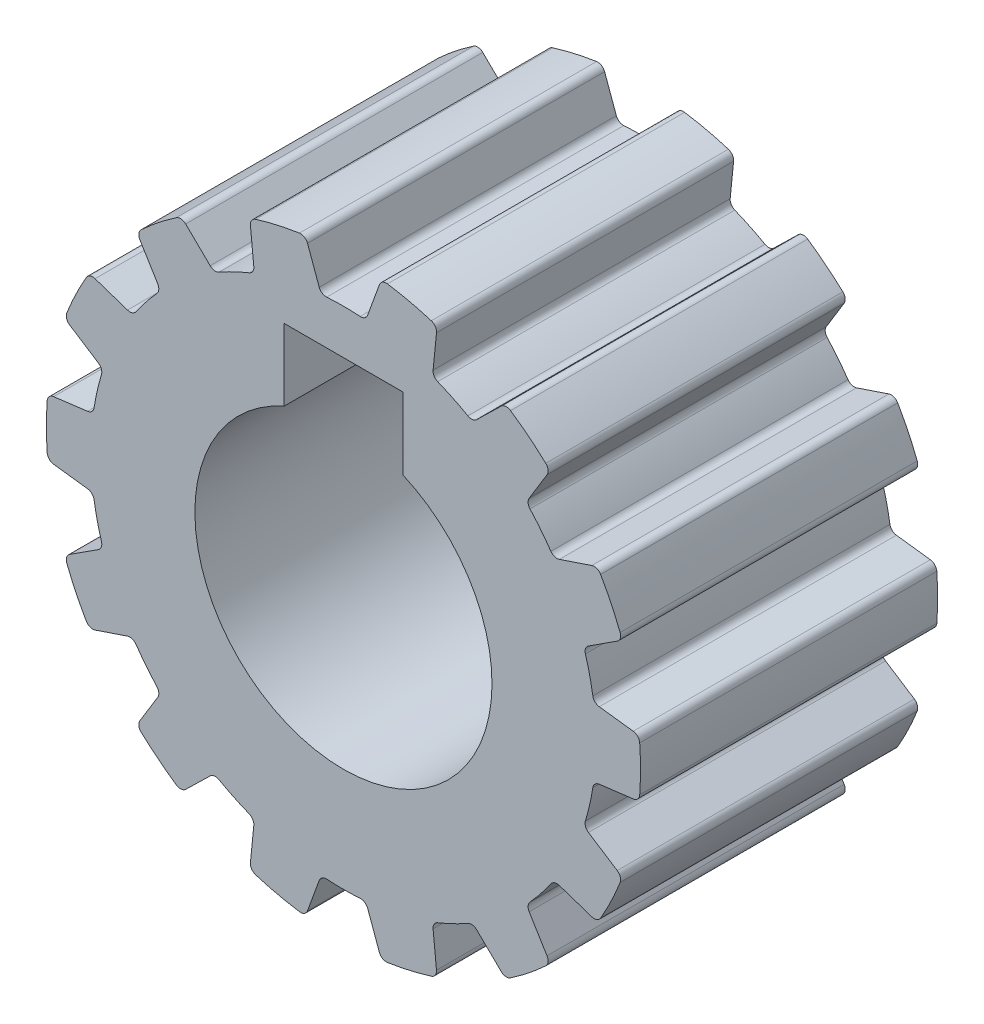
SolidWorks part; units mm, degrees
ref_plane "Front Plane" through (0, 0, 0) normal (0, 0, 1) x (1, 0, 0)
ref_plane "Top Plane" through (0, 0, 0) normal (0, 1, 0) x (1, 0, 0)
ref_plane "Right Plane" through (0, 0, 0) normal (1, 0, 0) x (0, 0, -1)
sketch "Sketch1" plane through (0, 0, 0) normal (0, 0, 1) x (1, 0, 0)
  line L0 (0, 0) -> (0, 15.3637) construction
  line L2 (-2, 7) -> (2, 7)
  line L3 (-2, 7) -> (-2, 4.5826)
  line L5 (2, 7) -> (2, 4.5826)
  circle A0 centre (0, 0) radius 10
  arc A1 (-2, 4.5826) -> (2, 4.5826) centre (0, 0) ccw
  dimension "D1" = 20
  dimension "D2" = 10
  dimension "D3" = 7
  dimension "D4" = 4
extrude "Boss-Extrude1" add sketch "Sketch1" along normal blind 10
sketch "Sketch2" plane through (0, 0, 10) normal (0, 0, 1) x (1, 0, 0)
  line L0 (0, 0) -> (0, 15.5433) construction
  line L2 (0.75, 8.4668) -> (1.2782, 9.918)
  line L3 (-0.75, 8.4668) -> (-1.2782, 9.918)
  circle A0 centre (0, 0) radius 10 construction
  arc A1 (1.2782, 9.918) -> (-1.2782, 9.918) centre (0, 0) ccw
  arc A2 (-0.75, 8.4668) -> (0.75, 8.4668) centre (0, 0) cw
  point P10 (0, 8.5)
  dimension "D1" = 20
  dimension "D2" = 20
  dimension "D3" = 1.5
  dimension "D4" = 8.5
extrude "Cut-Extrude1" cut sketch "Sketch2" against normal through all
pattern_circular "CirPattern1" count 14 over 360 about axis through (0, 0, 0) along (0, 0, 1) of "Cut-Extrude1"
fillet "Fillet1" radius 0.25 56 edges at (-9.3849, 3.4531, 5) (-8.0877, 2.6152, 5) (-8.4215, 1.1529, 5) (-9.9537, 0.9608, 5) (-9.9537, -0.9608, 5) (-8.4215, -1.1529, 5) (-8.0877, -2.6152, 5) (-9.3849, -3.4531, 5) (-8.5511, -5.1844, 5) (-7.0873, -4.6926, 5) (-6.152, -5.8654, 5) (-6.9573, -7.1831, 5) (-5.4548, -8.3812, 5) (-4.3494, -7.303, 5) (-2.9979, -7.9538, 5) (-3.1517, -9.4904, 5) (-1.2782, -9.918, 5) (-0.75, -8.4668, 5) (0.75, -8.4668, 5) (1.2782, -9.918, 5) (3.1517, -9.4904, 5) (2.9979, -7.9538, 5) (4.3494, -7.303, 5) (5.4548, -8.3812, 5) (6.9573, -7.1831, 5) (6.152, -5.8654, 5) (7.0873, -4.6926, 5) (8.5511, -5.1844, 5) (9.3849, -3.4531, 5) (8.0877, -2.6152, 5) (8.4215, -1.1529, 5) (9.9537, -0.9608, 5) (9.9537, 0.9608, 5) (8.4215, 1.1529, 5) (8.0877, 2.6152, 5) (9.3849, 3.4531, 5) (8.5511, 5.1844, 5) (7.0873, 4.6926, 5) (6.152, 5.8654, 5) (6.9573, 7.1831, 5) (5.4548, 8.3812, 5) (4.3494, 7.303, 5) (2.9979, 7.9538, 5) (3.1517, 9.4904, 5) (1.2782, 9.918, 5) (0.75, 8.4668, 5) (-0.75, 8.4668, 5) (-3.1517, 9.4904, 5) (-2.9979, 7.9538, 5) (-4.3494, 7.303, 5) (-5.4548, 8.3812, 5) (-6.9573, 7.1831, 5) (-6.152, 5.8654, 5) (-7.0873, 4.6926, 5) (-8.5511, 5.1844, 5) (-1.2782, 9.918, 5)
